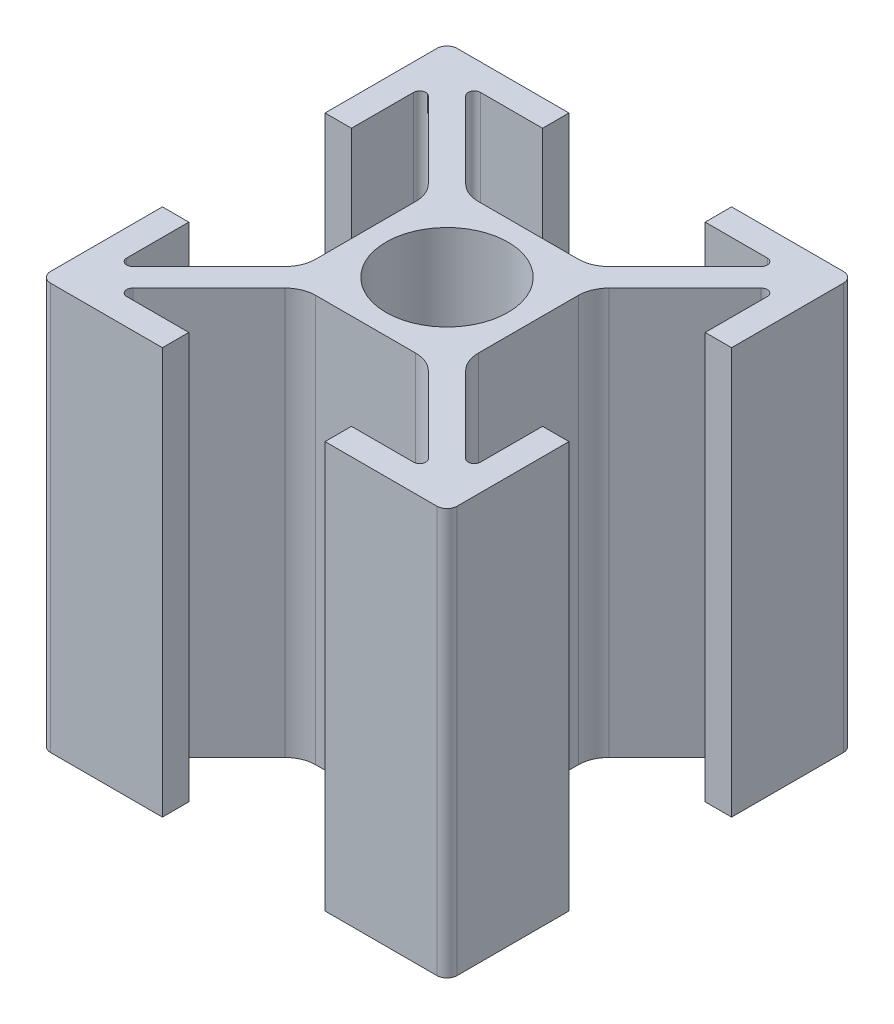
SolidWorks part; units mm, degrees
ref_plane "Plano frontal" through (0, 0, 0) normal (0, 0, 1) x (1, 0, 0)
ref_plane "Plano superior" through (0, 0, 0) normal (0, 1, 0) x (1, 0, 0)
ref_plane "Plano direito" through (0, 0, 0) normal (1, 0, 0) x (0, 0, -1)
sketch "Esboço1" plane through (0, 0, 0) normal (0, 1, 0) x (1, 0, 0)
  line L0 (-7.0565, 8.7) -> (-4, 8.7)
  line L1 (-4, 8.7) -> (-4, 10)
  line L2 (-4, 10) -> (-9.5, 10)
  line L3 (-10, 9.5) -> (-10, 4)
  line L4 (-10, 4) -> (-8.7, 4)
  line L5 (-8.7, 4) -> (-8.7, 7.0565)
  line L6 (-8.1879, 7.2686) -> (-4.4393, 3.5201)
  line L7 (-4, 2.4594) -> (-4, -2.4594)
  line L8 (-4.4393, -3.5201) -> (-8.1879, -7.2686)
  line L9 (-8.7, -7.0565) -> (-8.7, -4)
  line L10 (-8.7, -4) -> (-10, -4)
  line L11 (-10, -4) -> (-10, -9.5)
  line L12 (-9.5, -10) -> (-4, -10)
  line L13 (-4, -10) -> (-4, -8.7)
  line L14 (-4, -8.7) -> (-7.0565, -8.7)
  line L15 (-7.2686, -8.1879) -> (-3.5201, -4.4393)
  line L16 (-2.4594, -4) -> (2.4594, -4)
  line L17 (3.5201, -4.4393) -> (7.2686, -8.1879)
  line L18 (7.0565, -8.7) -> (4, -8.7)
  line L19 (4, -8.7) -> (4, -10)
  line L20 (4, -10) -> (9.5, -10)
  line L21 (10, -9.5) -> (10, -4)
  line L22 (10, -4) -> (8.7, -4)
  line L23 (8.7, -4) -> (8.7, -7.0565)
  line L24 (8.1879, -7.2686) -> (4.4393, -3.5201)
  line L25 (4, -2.4594) -> (4, 2.4594)
  line L26 (4.4393, 3.5201) -> (8.1879, 7.2686)
  line L27 (8.7, 7.0565) -> (8.7, 4)
  line L28 (8.7, 4) -> (10, 4)
  line L29 (10, 4) -> (10, 9.5)
  line L30 (9.5, 10) -> (4, 10)
  line L31 (4, 10) -> (4, 8.7)
  line L32 (4, 8.7) -> (7.0565, 8.7)
  line L33 (7.2686, 8.1879) -> (3.5201, 4.4393)
  line L34 (2.4594, 4) -> (-2.4594, 4)
  line L35 (-3.5201, 4.4393) -> (-7.2686, 8.1879)
  circle A0 centre (0, 0) radius 3
  arc A1 (-7.0565, 8.7) -> (-7.2686, 8.1879) centre (-7.0565, 8.4) ccw
  arc A2 (-9.5, 10) -> (-10, 9.5) centre (-9.5, 9.5) ccw
  arc A3 (-8.1879, 7.2686) -> (-8.7, 7.0565) centre (-8.4, 7.0565) ccw
  arc A4 (-4, 2.4594) -> (-4.4393, 3.5201) centre (-5.5, 2.4594) ccw
  arc A5 (-4.4393, -3.5201) -> (-4, -2.4594) centre (-5.5, -2.4594) ccw
  arc A6 (-8.7, -7.0565) -> (-8.1879, -7.2686) centre (-8.4, -7.0565) ccw
  arc A7 (-10, -9.5) -> (-9.5, -10) centre (-9.5, -9.5) ccw
  arc A8 (-7.2686, -8.1879) -> (-7.0565, -8.7) centre (-7.0565, -8.4) ccw
  arc A9 (-2.4594, -4) -> (-3.5201, -4.4393) centre (-2.4594, -5.5) ccw
  arc A10 (3.5201, -4.4393) -> (2.4594, -4) centre (2.4594, -5.5) ccw
  arc A11 (7.0565, -8.7) -> (7.2686, -8.1879) centre (7.0565, -8.4) ccw
  arc A12 (9.5, -10) -> (10, -9.5) centre (9.5, -9.5) ccw
  arc A13 (8.1879, -7.2686) -> (8.7, -7.0565) centre (8.4, -7.0565) ccw
  arc A14 (4, -2.4594) -> (4.4393, -3.5201) centre (5.5, -2.4594) ccw
  arc A15 (4.4393, 3.5201) -> (4, 2.4594) centre (5.5, 2.4594) ccw
  arc A16 (8.7, 7.0565) -> (8.1879, 7.2686) centre (8.4, 7.0565) ccw
  arc A17 (10, 9.5) -> (9.5, 10) centre (9.5, 9.5) ccw
  arc A18 (7.2686, 8.1879) -> (7.0565, 8.7) centre (7.0565, 8.4) ccw
  arc A19 (2.4594, 4) -> (3.5201, 4.4393) centre (2.4594, 5.5) ccw
  arc A20 (-3.5201, 4.4393) -> (-2.4594, 4) centre (-2.4594, 5.5) ccw
extrude "Ressalto-extrusão1" add sketch "Esboço1" along normal blind 20
